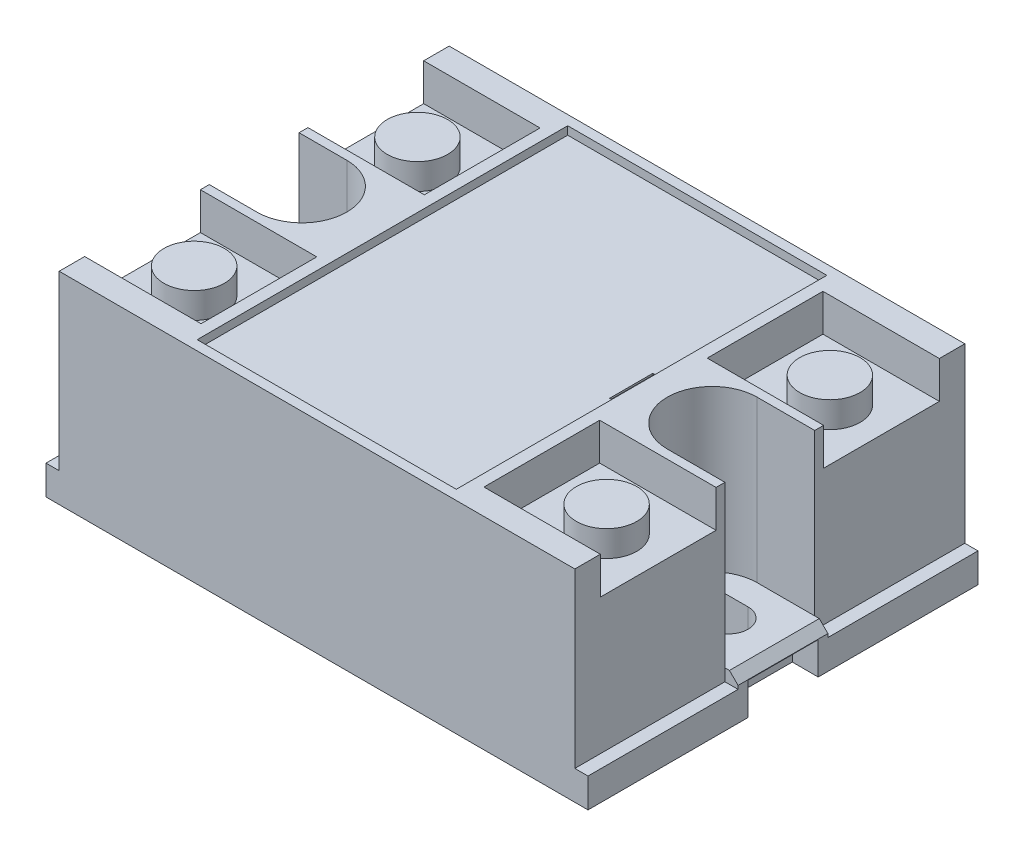
SolidWorks part; units mm, degrees
ref_plane "Front Plane" through (0, 0, 0) normal (0, 0, 1) x (1, 0, 0)
ref_plane "Top Plane" through (0, 0, 0) normal (0, 1, 0) x (1, 0, 0)
ref_plane "Right Plane" through (0, 0, 0) normal (1, 0, 0) x (0, 0, -1)
sketch "Sketch1" plane through (0, 0, 0) normal (0, 1, 0) x (1, 0, 0)
  line L1 (-31.375, -22.575) -> (31.375, -22.575)
  line L2 (-31.375, -22.575) -> (-31.375, 22.575)
  line L3 (-31.375, 22.575) -> (31.375, 22.575)
  line L4 (31.375, -22.575) -> (31.375, 22.575)
  line L5 (-31.375, -22.575) -> (31.375, 22.575) construction
  line L6 (-31.375, 22.575) -> (31.375, -22.575) construction
  point P0 (0, 0)
  dimension "D1" = 62.75
  dimension "D2" = 45.15
extrude "Boss-Extrude1" add sketch "Sketch1" along normal blind 23.4
sketch "Sketch2" plane through (0, 23.4, 0) normal (0, 1, 0) x (1, 0, 0)
  line L1 (-15, -21.45) -> (15, -21.45)
  line L2 (-15, -21.45) -> (-15, 21.45)
  line L3 (-15, 21.45) -> (15, 21.45)
  line L4 (15, -21.45) -> (15, 21.45)
  line L5 (-15, -21.45) -> (15, 21.45) construction
  line L6 (-15, 21.45) -> (15, -21.45) construction
  point P0 (0, 0)
  dimension "D1" = 30
  dimension "D2" = 42.9
extrude "Cut-Extrude1" cut sketch "Sketch2" against normal blind 0.95
sketch "Sketch3" plane through (0, 23.4, 0) normal (0, 1, 0) x (1, 0, 0)
  line L0 (-31.375, 22.575) -> (-31.375, -22.575) construction
  line L1 (-31.375, 19.625) -> (-16.375, 19.625)
  line L2 (-31.375, 19.625) -> (-31.375, 6.225)
  line L3 (-31.375, 6.225) -> (-16.375, 6.225)
  line L4 (-16.375, 19.625) -> (-16.375, 6.225)
  line L5 (-31.375, 0) -> (31.375, 0) construction
  line L6 (31.375, -22.575) -> (31.375, 22.575) construction
  line L7 (0, 22.575) -> (0, -22.575) construction
  line L8 (31.375, 22.575) -> (-31.375, 22.575) construction
  line L9 (-31.375, -22.575) -> (31.375, -22.575) construction
  line L10 (-16.375, -19.625) -> (-16.375, -6.225)
  line L11 (-31.375, -6.225) -> (-16.375, -6.225)
  line L12 (-31.375, -19.625) -> (-31.375, -6.225)
  line L13 (-31.375, -19.625) -> (-16.375, -19.625)
  line L14 (31.375, -19.625) -> (16.375, -19.625)
  line L15 (31.375, -19.625) -> (31.375, -6.225)
  line L16 (31.375, -6.225) -> (16.375, -6.225)
  line L17 (16.375, -19.625) -> (16.375, -6.225)
  line L18 (16.375, 19.625) -> (16.375, 6.225)
  line L19 (31.375, 6.225) -> (16.375, 6.225)
  line L20 (31.375, 19.625) -> (31.375, 6.225)
  line L21 (31.375, 19.625) -> (16.375, 19.625)
  dimension "D1" = 13.4
  dimension "D2" = 2.95
  dimension "D3" = 15
extrude "Cut-Extrude2" cut sketch "Sketch3" against normal blind 4.3
sketch "Sketch4" plane through (0, 19.1, 0) normal (0, 1, 0) x (1, 0, 0)
  line L0 (-23.875, 19.625) -> (-23.875, 6.225) construction
  line L1 (-16.375, 19.625) -> (-31.375, 19.625) construction
  line L2 (-31.375, 6.225) -> (-16.375, 6.225) construction
  line L3 (0, 22.575) -> (0, -22.575) construction
  line L4 (31.375, 22.575) -> (-31.375, 22.575) construction
  line L5 (-31.375, -22.575) -> (31.375, -22.575) construction
  line L6 (-31.375, 0) -> (31.375, 0) construction
  line L7 (-31.375, 6.225) -> (-31.375, -6.225) construction
  line L8 (31.375, -6.225) -> (31.375, 6.225) construction
  line L9 (-23.875, -19.625) -> (-23.875, -6.225) construction
  line L10 (23.875, -19.625) -> (23.875, -6.225) construction
  line L11 (23.875, 19.625) -> (23.875, 6.225) construction
  circle A0 centre (-23.875, 12.925) radius 3.5
  circle A1 centre (-23.875, -12.925) radius 3.5
  circle A2 centre (23.875, -12.925) radius 3.5
  circle A3 centre (23.875, 12.925) radius 3.5
  dimension "D1" = 7
extrude "Boss-Extrude2" add sketch "Sketch4" along normal blind 3
sketch "Sketch5" plane through (0, 23.4, 0) normal (0, 1, 0) x (1, 0, 0)
  line L0 (-31.375, 0) -> (-24.325, 0) construction
  line L3 (31.375, 0) -> (23.175, 0) construction
  line L4 (31.375, -6.225) -> (31.375, 6.225) construction
  line L5 (31.375, -5.2) -> (23.175, -5.2)
  line L6 (31.375, 5.2) -> (23.175, 5.2)
  line L7 (-31.375, 6.225) -> (-31.375, -6.225) construction
  line L8 (-31.375, 5.2) -> (-24.325, 5.2)
  line L9 (-31.375, -5.2) -> (-24.325, -5.2)
  arc A0 (31.375, -5.2) -> (31.375, 5.2) centre (31.375, 0) ccw
  arc A1 (23.175, 5.2) -> (23.175, -5.2) centre (23.175, 0) ccw
  arc A2 (-31.375, 5.2) -> (-31.375, -5.2) centre (-31.375, 0) ccw
  arc A3 (-24.325, -5.2) -> (-24.325, 5.2) centre (-24.325, 0) ccw
  point P4 (-27.85, 0)
  point P11 (27.275, 0)
  dimension "D1" = 10.4
  dimension "D2" = 13.4
  dimension "D3" = 12.25
extrude "Cut-Extrude3" cut sketch "Sketch5" against normal blind 18.6
sketch "Sketch6" plane through (0, 22.45, 0) normal (0, 1, 0) x (1, 0, 0)
  line L0 (31.375, 0) -> (0, 0) construction
  line L1 (31.375, -5.2) -> (31.375, 5.2) construction
  line L2 (14, 2.5) -> (14, -2.5)
  line L3 (15, -21.45) -> (15, 21.45) construction
  dimension "D1" = 1
  dimension "D2" = 5
extrude "Cut-Extrude-Thin1" cut sketch "Sketch6" against normal blind 1 and the other way through all thin
sketch "Sketch7" plane through (0, 4.8, 0) normal (0, 1, 0) x (1, 0, 0)
  line L0 (22.275, 0) -> (25.075, 0) construction
  line L1 (22.275, 2.25) -> (25.075, 2.25)
  line L2 (22.275, -2.25) -> (25.075, -2.25)
  line L3 (31.375, -5.2) -> (31.375, 5.2) construction
  arc A0 (22.275, 2.25) -> (22.275, -2.25) centre (22.275, 0) ccw
  arc A1 (25.075, -2.25) -> (25.075, 2.25) centre (25.075, 0) ccw
  point P3 (23.675, 0)
  dimension "D3" = 7.3
  dimension "D1" = 4.05
  dimension "D2" = 4.5
extrude "Cut-Extrude4" cut sketch "Sketch7" against normal through all
sketch "Sketch8" plane through (0, 4.8, 0) normal (0, 1, 0) x (1, 0, 0)
  line L0 (22.275, 0) -> (-31.375, 0) construction
  line L1 (-31.375, 5.2) -> (-31.375, -5.2) construction
  circle A0 centre (-23.825, 0) radius 2.25
  arc A3 (-24.325, -5.2) -> (-24.325, 5.2) centre (-24.325, 0) ccw construction
  dimension "D1" = 4.5
  dimension "D2" = 5.7
extrude "Cut-Extrude5" cut sketch "Sketch8" against normal through all
sketch "Sketch9" plane through (0, 23.4, 0) normal (0, 1, 0) x (1, 0, 0)
  line L0 (-31.375, -22.575) -> (31.375, -22.575) construction
  line L1 (-31.375, 22.575) -> (-29.85, 22.575)
  line L2 (-31.375, 22.575) -> (-31.375, -22.575)
  line L3 (-31.375, -22.575) -> (-29.85, -22.575)
  line L4 (-29.85, 22.575) -> (-29.85, -22.575)
  line L5 (0, 22.575) -> (0, -22.575) construction
  line L6 (31.375, 22.575) -> (-31.375, 22.575) construction
  line L7 (29.85, 22.575) -> (29.85, -22.575)
  line L8 (31.375, -22.575) -> (29.85, -22.575)
  line L9 (31.375, 22.575) -> (31.375, -22.575)
  line L10 (31.375, 22.575) -> (29.85, 22.575)
  dimension "D1" = 59.7
extrude "Cut-Extrude6" cut sketch "Sketch9" against normal blind 20
sketch "Sketch11" plane through (0, 3.4, 0) normal (0, 1, 0) x (1, 0, 0)
  line L0 (-31.375, 22.575) -> (-31.375, -22.575) construction
  line L1 (-29.85, 5.2) -> (-31.375, 5.2)
  line L2 (-29.85, 5.2) -> (-29.85, -5.2)
  line L3 (-29.85, -5.2) -> (-31.375, -5.2)
  line L4 (-31.375, 5.2) -> (-31.375, -5.2)
  line L5 (31.375, -22.575) -> (31.375, 22.575) construction
  line L6 (29.85, 5.2) -> (31.375, 5.2)
  line L7 (29.85, 5.2) -> (29.85, -5.2)
  line L8 (29.85, -5.2) -> (31.375, -5.2)
  line L9 (31.375, 5.2) -> (31.375, -5.2)
  line L10 (29.85, 22.575) -> (29.85, -22.575) construction
extrude "Boss-Extrude3" add sketch "Sketch11" along normal up to surface (1.4 mm away) up to face at (-25.7875, 4.8, 0)
chamfer "Chamfer1" distance 1 angle 45 2 edges at (31.375, 4.8, 0) (-31.375, 4.8, 0)
sketch "Sketch10" plane through (0, 0, 0) normal (0, -1, 0) x (1, 0, 0)
  line L0 (0, 22.575) -> (0, -22.575) construction
  line L1 (-31.375, 22.575) -> (31.375, 22.575) construction
  line L2 (31.375, -22.575) -> (-31.375, -22.575) construction
  line L3 (-31.375, 0) -> (31.375, 0) construction
  line L4 (-31.375, -22.575) -> (-31.375, 22.575) construction
  line L5 (31.375, 22.575) -> (31.375, -22.575) construction
  line L6 (-28.375, 4.075) -> (-31.375, -4.075) construction
  line L7 (28.375, -4.075) -> (31.375, -4.075)
  line L8 (28.375, -4.075) -> (28.375, 4.075)
  line L9 (28.375, 4.075) -> (31.375, 4.075)
  line L10 (31.375, -4.075) -> (31.375, 4.075)
  line L11 (28.375, -4.075) -> (31.375, 4.075) construction
  line L12 (28.375, 4.075) -> (31.375, -4.075) construction
  line L13 (-28.375, -4.075) -> (-31.375, 4.075) construction
  line L14 (-31.375, -4.075) -> (-31.375, 4.075)
  line L15 (-28.375, 4.075) -> (-31.375, 4.075)
  line L16 (-28.375, -4.075) -> (-28.375, 4.075)
  line L17 (-28.375, -4.075) -> (-31.375, -4.075)
  point P12 (29.875, 0)
  point P21 (-29.875, 0)
  dimension "D1" = 8.15
  dimension "D2" = 3
extrude "Cut-Extrude7" cut sketch "Sketch10" against normal blind 3.75
sketch "Sketch13" plane through (0, 22.45, 0) normal (0, 1, 0) x (1, 0, 0)
